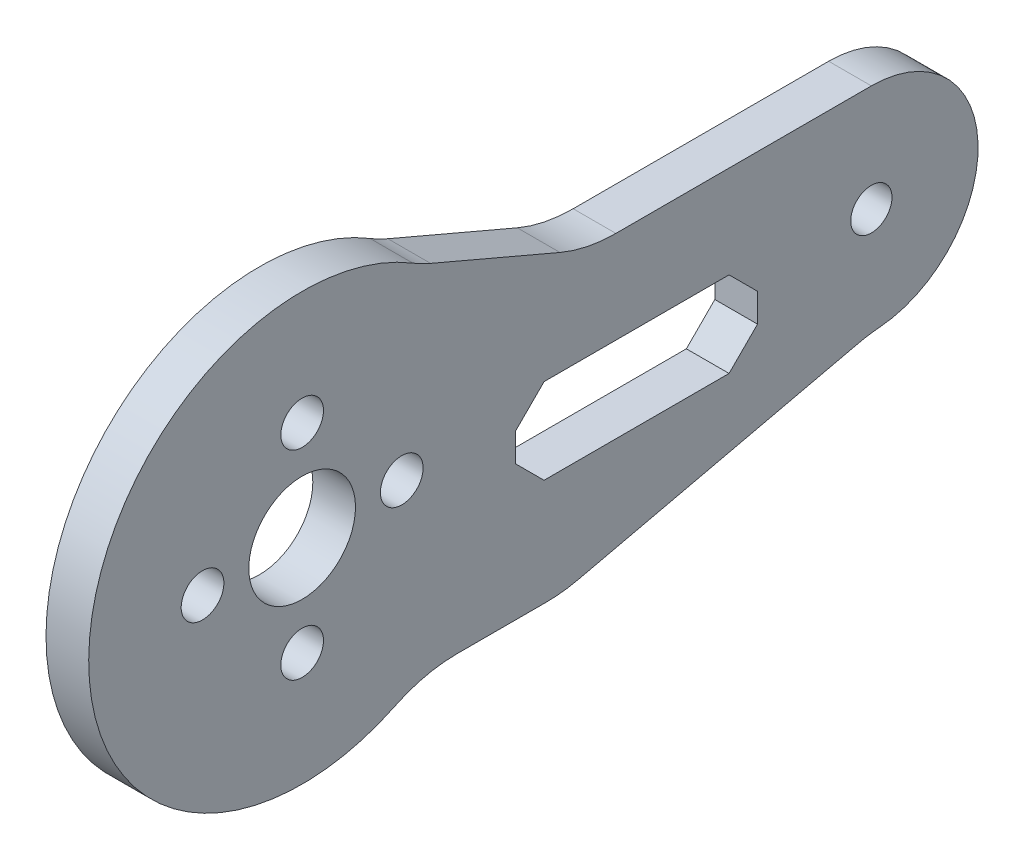
SolidWorks part; units mm, degrees
ref_plane "Front Plane" through (0, 0, 0) normal (0, 0, 1) x (1, 0, 0)
ref_plane "Top Plane" through (0, 0, 0) normal (0, 1, 0) x (1, 0, 0)
ref_plane "Right Plane" through (0, 0, 0) normal (1, 0, 0) x (0, 0, -1)
sketch "Sketch1" plane through (0, 0, 0) normal (1, 0, 0) x (0, 0, -1)
  line L0 (0, 0) -> (7.675, 0) construction
  line L2 (10.675, 0) -> (13.675, 0) construction
  line L3 (0, 0) -> (40, 0) construction
  line L4 (40, -7.5) -> (18.2916, -12.5)
  line L5 (18.2916, -12.5) -> (8.2916, -12.5)
  line L6 (40, 7.5) -> (20, 7.5)
  line L7 (20, 7.5) -> (8.2916, 12.5)
  circle A0 centre (0, 0) radius 3.75
  circle A1 centre (0, 7) radius 1.5
  circle A2 centre (0, -7) radius 1.5
  circle A3 centre (0, 0) radius 15
  circle A4 centre (-7, 0) radius 1.5
  circle A5 centre (7, 0) radius 1.5
  circle A14 centre (40, 0) radius 7.5
  circle A15 centre (40, 0) radius 1.45
  point P32 (0, 0)
  dimension "D1" = 7.5
  dimension "D2" = 7.675
  dimension "D4" = 7
  dimension "D5" = 30
  dimension "D8" = 15
  dimension "D9" = 2.9
  dimension "D12" = 20
  dimension "D15" = 3
  dimension "D16" = 3
  dimension "D17" = 3
  dimension "D18" = 3
  dimension "D3" = 7
  dimension "D7" = 40
  dimension "D10" = 10
  dimension "D11" = 12.5
  dimension "D13" = 12.5
  dimension "D6" = 7
  dimension "D14" = 7
extrude "Boss-Extrude1" add sketch "Sketch1" along normal mid plane 3
fillet "Fillet1" radius 10 5 edges at (0, -12.5, -18.2916) (0, 12.5, -8.2916) (0, 7.5, -20) (0, -7.5, -40) (0, -12.5, -8.2916)
sketch "Sketch2" plane through (1.5, 0, 0) normal (1, 0, 0) x (0, 0, -1)
  line L0 (0, 0) -> (40, 0) construction
  line L1 (40, 7.5) -> (22.0458, 7.5) construction
  line L2 (17, 1) -> (30, 1)
  line L3 (15, -1) -> (15, -3)
  line L4 (24.5, -1.5) -> (24.5, 0) construction
  line L5 (17, -5) -> (30, -5)
  line L6 (32, -1) -> (32, -3)
  line L7 (17.1548, -12.5) -> (10.8972, -12.5) construction
  line L8 (15, -1) -> (17, 1)
  line L9 (15, -3) -> (17, -5)
  line L10 (30, 1) -> (32, -1)
  line L11 (30, -5) -> (32, -3)
  point P4 (15, 1)
  point P5 (32, -5)
  point P6 (15, -5)
  point P7 (32, 1)
  dimension "D2" = 7.5
  dimension "D1" = 6.5
  dimension "D3" = 15.5
  dimension "D4" = 1.5
  dimension "D5" = 8
  dimension "D6" = 17
extrude "Cut-Extrude1" cut sketch "Sketch2" against normal blind 3
